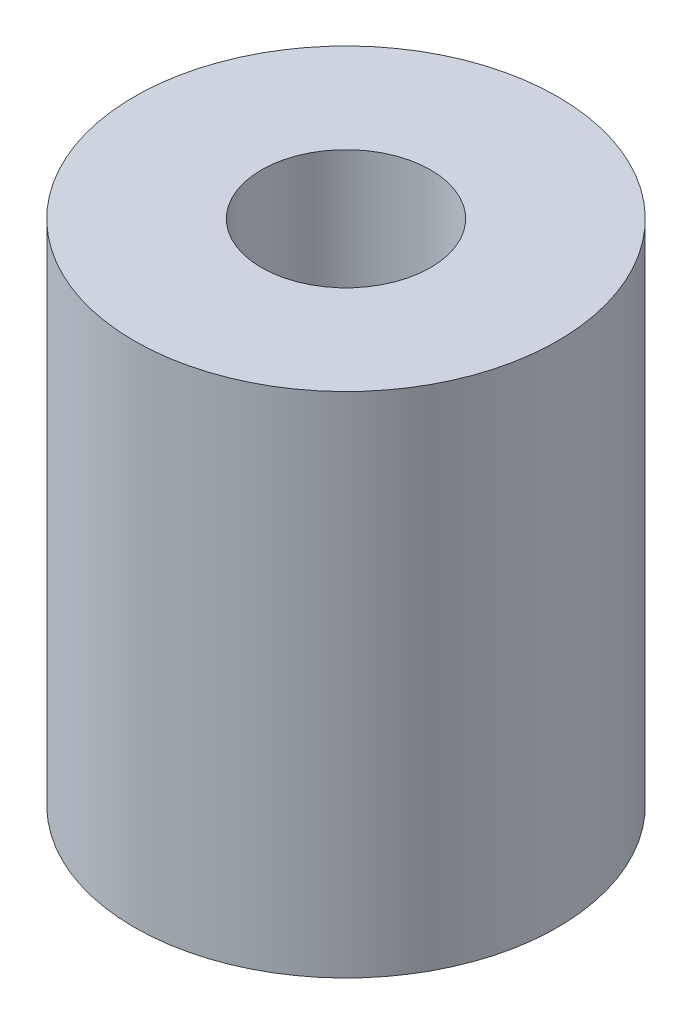
SolidWorks part; units mm, degrees
ref_plane "Front Plane" through (0, 0, 0) normal (0, 0, 1) x (1, 0, 0)
ref_plane "Top Plane" through (0, 0, 0) normal (0, 1, 0) x (1, 0, 0)
ref_plane "Right Plane" through (0, 0, 0) normal (1, 0, 0) x (0, 0, -1)
sketch "Sketch2" plane through (0, 0, 0) normal (0, 1, 0) x (1, 0, 0)
  circle A0 centre (0, 0) radius 2.5
  circle A1 centre (0, 0) radius 1
  dimension "D1" = 2
  dimension "D2" = 5
extrude "Boss-Extrude1" add sketch "Sketch2" along normal blind 6
